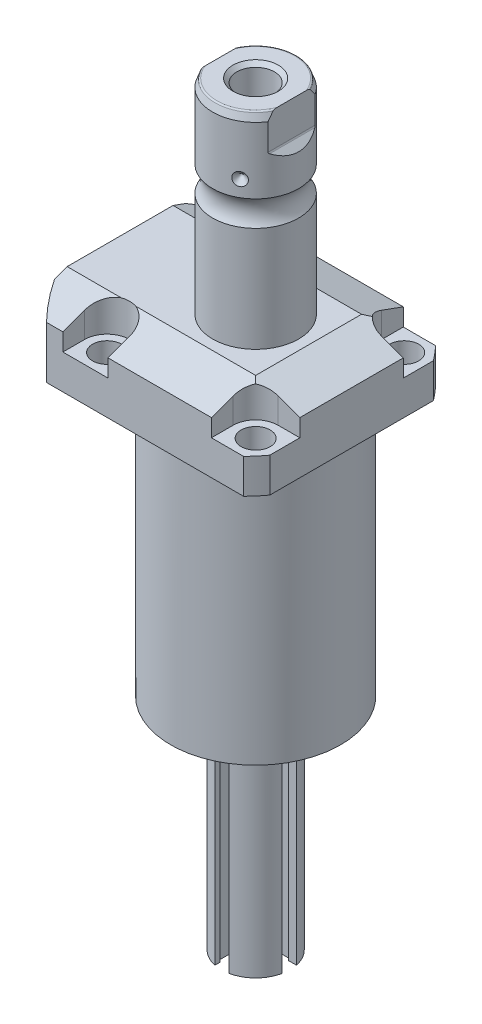
SolidWorks part; units mm, degrees
material "Alloy Steel"
ref_plane "Front Plane" through (0, 0, 0) normal (0, 0, 1) x (1, 0, 0)
ref_plane "Top Plane" through (0, 0, 0) normal (0, 1, 0) x (1, 0, 0)
ref_plane "Right Plane" through (0, 0, 0) normal (1, 0, 0) x (0, 0, -1)
sketch "Sketch1" plane through (0, 0, 0) normal (0, -1, 0) x (0, 0, 1)
  line L0 (-35.433, 50.063) -> (35.433, 50.063)
  line L1 (35.433, 50.063) -> (35.433, -35.433)
  line L2 (35.433, -35.433) -> (-35.433, -35.433)
  line L3 (-35.433, -35.433) -> (-35.433, 50.063)
  line L4 (0, 0) -> (0, -60.6467) construction
  dimension "D1" = 35.433
  dimension "D2" = 85.496
  dimension "D3" = 70.866
extrude "Extrude1" add sketch "Sketch1" against normal blind 122.047
sketch "Sketch2" plane through (0, 0, 0) normal (0, -1, 0) x (1, 0, 0)
  circle A0 centre (-5.4102, 0) radius 50.8
  dimension "D1" = 101.6
  dimension "D2" = 5.4102
extrude "Cut-Extrude1" cut sketch "Sketch2" against normal through all flip side to cut
sketch "Sketch3" plane through (0, 0, 0) normal (1, 0, 0) x (0, 0, -1)
  line L0 (31.3945, 0) -> (31.3945, 97.028)
  line L1 (31.3945, 97.028) -> (76.5937, 97.028)
  line L2 (76.5937, 97.028) -> (76.5937, 0)
  line L3 (76.5937, 0) -> (31.3945, 0)
  line L4 (0, -93.345) -> (0, 4.445) construction
  line L5 (24.2233, 0) -> (-24.2233, 0) construction
  dimension "D1" = 62.789
  dimension "D2" = 153.1874
  dimension "D3" = 97.028
revolve "Cut-Revolve1" cut sketch "Sketch3" angle 360 about L4
fillet "Fillet1" radius 0.381 1 edges at (0, 97.028, -31.3945)
sketch "Sketch4" plane through (0, 122.047, 0) normal (0, 1, 0) x (-1, 0, 0)
  line L0 (-35.433, -30.2072) -> (-35.433, 30.2072) construction
  line L1 (41.8127, 35.433) -> (-30.9923, 35.433) construction
  line L2 (-19.1008, -35.433) -> (-19.1008, -27.432)
  line L3 (-35.433, -35.433) -> (-19.1008, -35.433)
  line L4 (-35.433, -19.1008) -> (-35.433, -35.433)
  line L5 (-27.432, -19.1008) -> (-35.433, -19.1008)
  line L6 (35.7632, -35.433) -> (19.1008, -35.433)
  line L7 (19.1008, 35.433) -> (19.1008, 27.432)
  line L8 (35.7632, 35.433) -> (35.7632, 27.432)
  line L9 (35.7632, 35.433) -> (19.1008, 35.433)
  line L10 (-27.432, 19.1008) -> (-35.433, 19.1008)
  line L11 (-35.433, 19.1008) -> (-35.433, 35.433)
  line L12 (-35.433, 35.433) -> (-19.1008, 35.433)
  line L13 (-19.1008, 35.433) -> (-19.1008, 27.432)
  line L14 (-48.9217, 0) -> (49.4551, 0) construction
  line L15 (35.7632, -35.433) -> (35.7632, -27.432)
  line L16 (19.1008, -35.433) -> (19.1008, -27.432)
  arc A0 (19.1008, -27.432) -> (35.7632, -27.432) centre (27.432, -27.432) cw
  arc A1 (-27.432, -19.1008) -> (-19.1008, -27.432) centre (-27.432, -27.432) cw
  arc A2 (-27.432, 19.1008) -> (-19.1008, 27.432) centre (-27.432, 27.432) ccw
  arc A3 (19.1008, 27.432) -> (35.7632, 27.432) centre (27.432, 27.432) ccw
  dimension "D2" = 8.3312
  dimension "D1" = 27.432
  dimension "D3" = 27.432
  dimension "D4" = 54.864
extrude "Cut-Extrude2" cut sketch "Sketch4" against normal blind 12.243
sketch "Sketch5" plane through (0, 0, 0) normal (1, 0, 0) x (0, 0, -1)
  line L0 (-19.558, 122.047) -> (-35.433, 116.269)
  line L1 (0, 0) -> (0, 154.1081) construction
  line L2 (-19.558, 122.047) -> (-35.433, 122.047)
  line L3 (-35.433, 122.047) -> (-35.433, 116.269)
  dimension "D1" = 15.875
  dimension "D2" = 20
extrude "Cut-Extrude9" cut sketch "Sketch5" against normal through all and the other way through all
mirror "Mirror1" about plane through (0, 0, 0) normal (0, 0, 1) of "Cut-Extrude9"
sketch "Sketch9" plane through (0, 0, 0) normal (0, 0, 1) x (1, 0, 0)
  line L0 (19.558, 122.047) -> (35.433, 116.269)
  line L1 (35.433, 116.269) -> (35.433, 122.047)
  line L2 (35.433, 122.047) -> (19.558, 122.047)
  dimension "D1" = 15.875
  dimension "D2" = 20
extrude "Cut-Extrude7" cut sketch "Sketch9" against normal through all and the other way through all
ref_plane "Plane14" through (-35.0774, 0, 0) normal (1, 0, 0) x (0, 0, -1)
sketch "Sketch20" plane through (-35.0774, 88.9, -18.1102) normal (1, 0, 0) x (0, 1, 0)
  line L0 (-88.9, 18.1102) -> (39.8401, 18.1102) construction
  line L1 (-7.2797, 32.639) -> (36.9042, 32.639) construction
  line L2 (8.128, 38.3413) -> (9.5758, 38.3413)
  line L3 (8.128, -6.1131) -> (8.128, 42.3335) construction
  line L4 (9.5758, 38.3413) -> (9.5758, 35.8902)
  line L5 (9.5758, 35.8902) -> (10.5918, 35.8902)
  line L6 (10.5918, 35.8902) -> (10.5918, 33.8836)
  line L7 (10.5918, 33.8836) -> (21.5646, 33.8836)
  line L8 (21.5646, 33.8836) -> (21.5646, 32.639)
  line L9 (21.5646, 32.639) -> (8.128, 32.639)
  line L10 (8.128, 38.3413) -> (8.128, 32.639)
  dimension "D1" = 14.5288
  dimension "D2" = 11.4046
  dimension "D3" = 1.4478
  dimension "D4" = 6.5024
  dimension "D5" = 1.016
  dimension "D6" = 2.4892
  dimension "D7" = 10.9728
revolve "Cut-Revolve4" cut sketch "Sketch20" angle 360 about L1
mirror "Mirror10" about plane through (0, 0, 0) normal (0, 0, 1) of "Cut-Revolve4"
sketch "Sketch10" plane through (-35.0774, 88.9, -18.1102) normal (1, 0, 0) x (0, 1, 0)
  line L0 (-1.0325, 3.5814) -> (1.5659, 3.5814) construction
  line L1 (21.5646, 4.826) -> (10.5918, 4.826) construction
  line L2 (10.5918, 2.3368) -> (21.5646, 2.3368) construction
  line L4 (8.128, -12.097) -> (8.128, 48.3174) construction
  circle A0 centre (8.3947, 8.1026) radius 1.1811
  dimension "D1" = 2.3622
  dimension "D2" = 0.2667
  dimension "D3" = 9.0424
revolve "Revolve4" add sketch "Sketch10" angle 360 about L0
mirror "Mirror12" about plane through (0, 0, 0) normal (0, 0, 1) of bodies 135
sketch "Sketch15" plane through (0, 0, 0) normal (1, 0, 0) x (0, 0, -1)
  line L0 (0, 122.047) -> (15.875, 122.047)
  line L1 (15.875, 122.047) -> (15.875, 160.7481)
  line L2 (15.875, 170.1623) -> (15.875, 194.6402)
  line L3 (14.8118, 197.5612) -> (0, 197.5612)
  line L4 (0, 197.5612) -> (0, 122.047)
  line L5 (0, 250.2908) -> (0, 28.9095) construction
  line L6 (19.558, 122.047) -> (-19.558, 122.047) construction
  line L7 (14.8118, 197.5612) -> (15.875, 194.6402)
  line L9 (24.2233, 97.028) -> (35.433, 97.028) construction
  arc A0 (15.875, 170.1623) -> (15.875, 160.7481) centre (22.2504, 165.4552) ccw
  dimension "D2" = 20
  dimension "D4" = 7.9248
  dimension "D6" = 28.6512
  dimension "D1" = 100.5332
  dimension "D3" = 31.75
  dimension "D5" = 32.106
  dimension "D7" = 2.921
revolve "Revolve3" add sketch "Sketch15" angle 360 about L5
hole_wizard "Hole1" positions "Sketch18" profile "Sketch17" legacy end condition up to next
sketch "Sketch18" plane through (0, 109.804, 0) normal (0, 1, 0) x (-1, 0, 0)
  arc A0 (35.7632, -27.432) -> (19.1008, -27.432) centre (27.432, -27.432) ccw construction
  arc A1 (19.1008, 27.432) -> (35.7632, 27.432) centre (27.432, 27.432) ccw construction
  arc A2 (-27.432, 19.1008) -> (-19.1008, 27.432) centre (-27.432, 27.432) ccw construction
  arc A3 (-19.1008, -27.432) -> (-27.432, -19.1008) centre (-27.432, -27.432) ccw construction
  point P0 (-27.432, -27.432)
  point P1 (-27.432, 27.432)
  point P3 (27.432, 27.432)
  point P5 (27.432, -27.432)
sketch "Sketch17" plane through (27.432, 109.804, -27.432) normal (1, 0, 0) x (0, 0, 1)
  line L0 (0, 0) -> (0, 12.776)
  line L1 (0, 12.776) -> (5.3594, 12.776)
  line L2 (5.3594, 12.776) -> (5.3594, 0)
  line L3 (5.3594, 0) -> (0, 0)
  line L4 (0, 110) -> (0, -10) construction
  dimension "Diameter" = 10.7188
  dimension "Depth" = 12.776
chamfer "Chamfer1" distance 0.635 angle 45 2 edges at (-35.0774, 99.4918, 13.2842) (-35.0774, 99.4918, -13.2842)
ref_plane "Plane15" through (0, 109.5248, 0) normal (0, -1, 0) x (1, 0, 0)
sketch "Sketch21" plane through (0, 109.5248, 0) normal (0, -1, 0) x (1, 0, 0)
  line L0 (-57.5495, -12.9794) -> (-2.9353, -12.9794) construction
  line L1 (-50.063, -1.9304) -> (-49.809, -1.9304)
  line L2 (-49.809, -1.9304) -> (-49.809, -6.7564)
  line L3 (-49.809, -6.7564) -> (-47.2563, -7.4404)
  line L4 (-46.6957, -8.001) -> (-30.759, -8.001)
  line L5 (-30.759, -8.001) -> (-30.759, -12.9794)
  line L6 (-30.759, -12.9794) -> (-50.063, -12.9794)
  line L7 (-50.063, 24.2233) -> (-50.063, -24.2233) construction
  line L8 (-50.063, -12.9794) -> (-50.063, -1.9304)
  line L9 (-47.2563, -7.4404) -> (-46.6957, -8.001)
  dimension "D1" = 12.9794
  dimension "D2" = 0.254
  dimension "D3" = 22.098
  dimension "D4" = 45
  dimension "D5" = 2.5527
  dimension "D6" = 9.9568
  dimension "D7" = 19.05
  dimension "D8" = 15
  dimension "D9" = 12.446
revolve "Cut-Revolve5" cut sketch "Sketch21" angle 360 about L0
mirror "Mirror13" about plane through (0, 0, 0) normal (0, 0, 1) of "Cut-Revolve5"
fillet "Fillet2" radius 0.635 1 edges at (0, 197.5612, 14.8118)
sketch "Sketch26" plane through (0, 0, 0) normal (0, 0, 1) x (1, 0, 0)
  line L0 (-39.772, 176.1232) -> (35.3173, 176.1232) construction
  line L1 (-15.875, 178.5362) -> (-13.462, 176.1232)
  line L2 (-15.875, 194.6402) -> (-15.875, 170.1623) construction
  line L3 (-13.462, 176.1232) -> (-15.875, 176.1232)
  line L4 (-15.875, 176.1232) -> (-15.875, 178.5362)
  arc A0 (-15.875, 160.7481) -> (-15.875, 170.1623) centre (-22.2504, 165.4552) ccw construction
  dimension "D1" = 45
  dimension "D2" = 4.826
  dimension "D3" = 10.668
revolve "Cut-Revolve7" cut sketch "Sketch26" angle 360 about L0
pattern_circular "CirPattern1" count 3 over 360 about axis through (0, 250.2908, 0) along (0, 1, 0) of "Cut-Revolve7"
hole_wizard "Hole2" positions "Sketch28" profile "Sketch27" legacy
sketch "Sketch28" plane through (0, 197.5612, 0) normal (0, 1, 0) x (-1, 0, 0)
  circle A0 centre (0, 0) radius 15.875 construction
  point P0 (0, 0)
sketch "Sketch27" plane through (0, 197.5612, 0) normal (1, 0, 0) x (0, 0, 1)
  line L0 (0, 0) -> (0, 28.8121)
  line L1 (0, 28.8121) -> (6.9469, 24.638)
  line L2 (6.9469, 24.638) -> (6.9469, 0)
  line L4 (6.9469, 0) -> (0, 0)
  line L6 (0, 28.8121) -> (-6.9469, 24.638) construction
  line L7 (0, -4.2442) -> (0, 117.3081) construction
  dimension "Diameter" = 13.8938
  dimension "Depth" = 24.638
  dimension "Drill Angle" = 118
sketch "Sketch29" plane through (0, 0, 0) normal (0, 0, 1) x (1, 0, 0)
  line L0 (0, 0) -> (0, 192.0172) construction
  line L1 (13.284, 197.5612) -> (13.284, 184.8612)
  line L2 (14.3672, 197.5612) -> (-14.3672, 197.5612) construction
  line L3 (13.5072, 184.3224) -> (16.332, 181.4976)
  line L5 (16.332, 181.4976) -> (16.332, 197.5612)
  line L6 (16.332, 197.5612) -> (13.284, 197.5612)
  line L7 (-16.332, 197.5612) -> (-13.284, 197.5612)
  line L8 (-16.332, 181.4976) -> (-16.332, 197.5612)
  line L9 (-13.5072, 184.3224) -> (-16.332, 181.4976)
  line L10 (-13.284, 197.5612) -> (-13.284, 184.8612)
  arc A0 (13.284, 184.8612) -> (13.5072, 184.3224) centre (14.046, 184.8612) ccw
  arc A1 (-13.284, 184.8612) -> (-13.5072, 184.3224) centre (-14.046, 184.8612) cw
  dimension "D2" = 0.762
  dimension "D1" = 45
  dimension "D3" = 26.568
  dimension "D4" = 12.7
  dimension "D5" = 3.048
extrude "Cut-Extrude10" cut sketch "Sketch29" against normal through all and the other way through all
chamfer "Chamfer2" distance 1.4351 angle 45 1 edges at (0, 197.5612, 6.9469)
sketch "Sketch30" plane through (0, 0, 0) normal (0, 0, 1) x (1, 0, 0)
  line L0 (0, 75.4045) -> (0, 27.1273) construction
  line L2 (0, 0) -> (22.225, 0)
  line L3 (-31.3945, 0) -> (31.3945, 0) construction
  line L4 (22.225, 0) -> (22.225, -2.54)
  line L5 (22.225, -2.54) -> (12.7, -2.54)
  line L6 (12.7, -2.54) -> (12.7, -81.28)
  line L7 (12.7, -81.28) -> (0, -81.28)
  line L8 (0, -81.28) -> (0, 0)
  dimension "D1" = 44.45
  dimension "D2" = 25.4
  dimension "D3" = 2.54
  dimension "D4" = 81.28
revolve "Revolve5" add sketch "Sketch30" angle 360 about L0
sketch "Sketch33" plane through (0, -2.54, 0) normal (0, -1, 0) x (1, 0, 0)
  circle A0 centre (0, 0) radius 19.431 construction
  circle A2 centre (19.431, 0) radius 2.7051
  dimension "D1" = 38.862
  dimension "D2" = 5.4102
extrude "Boss-Extrude1" add sketch "Sketch33" along normal blind 2.9972
pattern_circular "CirPattern2" count 3 over 360 about axis through (0, 0, 0) along (0, 1, 0) of "Boss-Extrude1"
sketch "Sketch34" plane through (0, -81.28, 0) normal (0, -1, 0) x (1, 0, 0)
  line L2 (13.335, -2.6416) -> (9.525, -2.6416)
  line L3 (9.525, -2.6416) -> (9.525, -3.4925)
  line L4 (9.525, -3.4925) -> (6.223, -3.4925)
  line L5 (6.223, -3.4925) -> (6.223, 3.4925)
  line L6 (6.223, 3.4925) -> (10.5463, 3.4925)
  line L7 (10.5463, 3.4925) -> (10.5463, 2.6416)
  line L8 (10.5463, 2.6416) -> (13.335, 2.6416)
  line L9 (13.335, 2.6416) -> (13.335, -2.6416)
  line L10 (47.0228, 0) -> (-47.0228, 0) construction
  line L11 (0, -38.9763) -> (0, 38.9763) construction
  dimension "D1" = 6.985
  dimension "D2" = 3.4925
  dimension "D3" = 5.2832
  dimension "D4" = 2.6416
  dimension "D5" = 6.223
  dimension "D6" = 3.302
  dimension "D7" = 3.81
extrude "Cut-Extrude11" cut sketch "Sketch34" against normal blind 70.612
pattern_circular "CirPattern3" count 4 over 360 about axis through (0, 0, 0) along (0, 1, 0) of "Cut-Extrude11"
sketch "Sketch35" plane through (0, 0, 6.223) normal (0, 0, 1) x (1, 0, 0)
  line L0 (-2.6416, -10.668) -> (2.6416, -10.668) construction
  circle A0 centre (0, -10.668) radius 3.4925
  dimension "D1" = 6.985
extrude "Cut-Extrude15" cut sketch "Sketch35" along normal blind 7.62
pattern_circular "CirPattern4" count 4 over 360 about axis through (0, 75.4045, 0) along (0, 1, 0) of "Cut-Extrude15"
sketch "Sketch37" plane through (0, -5.5372, 0) normal (0, -1, 0) x (1, 0, 0)
  line L0 (19.431, 2.7051) -> (19.431, -2.7051) construction
  line L1 (16.7259, 0) -> (22.1361, 0) construction
  line L2 (19.431, 1.2446) -> (20.1473, 1.2446)
  line L3 (20.1473, 1.2446) -> (20.8659, 0)
  line L4 (20.8659, 0) -> (20.1473, -1.2446)
  line L5 (20.1473, -1.2446) -> (18.7117, -1.2446)
  line L6 (18.7117, -1.2446) -> (17.9931, 0)
  line L7 (17.9931, 0) -> (18.7117, 1.2446)
  line L8 (18.7117, 1.2446) -> (19.431, 1.2446)
  circle A0 centre (19.431, 0) radius 2.7051 construction
  circle A1 centre (19.431, 0) radius 2.7051 construction
  dimension "D1" = 30
  dimension "D2" = 30
  dimension "D3" = 30
  dimension "D4" = 30
  dimension "D5" = 2.4892
  dimension "D6" = 1.2446
  dimension "D7" = 2.8727
  dimension "D8" = 0.7163
extrude "Cut-Extrude16" cut sketch "Sketch37" against normal blind 1.27
pattern_circular "CirPattern5" count 3 over 360 about axis through (0, 0, 0) along (0, 1, 0) of "Cut-Extrude16"
sketch "Sketch39" plane through (0, -2.54, 0) normal (0, -1, 0) x (1, 0, 0)
  circle A0 centre (19.431, 0) radius 1.7272
  dimension "D1" = 3.4544
extrude "Cut-Extrude17" cut sketch "Sketch39" against normal blind 2.54
pattern_circular "CirPattern6" count 12 over 360 about axis through (0, 0, 0) along (0, 1, 0) of "Cut-Extrude17"
